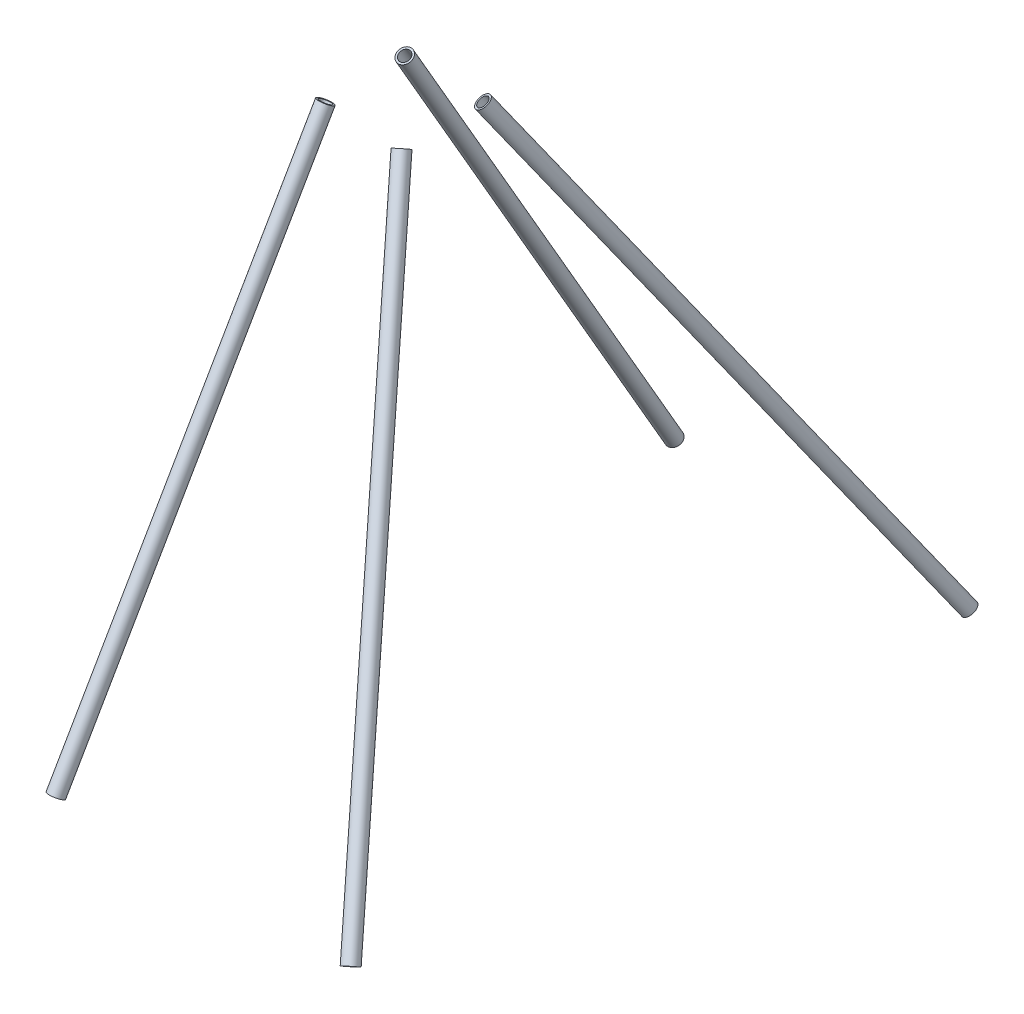
SolidWorks part; units mm, degrees
material "6061-T6 (SS)"
ref_plane "Front Plane" through (0, 0, 0) normal (0, 0, 1) x (1, 0, 0)
ref_plane "Top Plane" through (0, 0, 0) normal (0, 1, 0) x (1, 0, 0)
ref_plane "Right Plane" through (0, 0, 0) normal (1, 0, 0) x (0, 0, -1)
sketch "Sketch1" plane through (0, 0, 0) normal (1, 0, 0) x (0, 0, -1)
  line L0 (-31.75, 0) -> (31.75, 0) construction
  line L1 (31.75, 0) -> (266.7, -406.4)
  line L3 (-31.75, 0) -> (-266.7, -406.4)
  dimension "D1" = 406.4
  dimension "D2" = 533.4
  dimension "D3" = 63.5
ref_plane "Plane1" through (0, -406.4, 0) normal (0, 1, 0) x (1, 0, 0)
sketch "Sketch2" plane through (0, -406.4, 0) normal (0, 1, 0) x (1, 0, 0)
  line L0 (0, -266.7) -> (254, -266.7) construction
  line L2 (0, 266.7) -> (254, 266.7) construction
  dimension "D1" = 254
sketch "Sketch3" plane through (0, 0, 0) normal (0, 1, 0) x (1, 0, 0)
  line L1 (0, -31.75) -> (63.5, -31.75) construction
  line L2 (0, -31.75) -> (0, 31.75) construction
  line L3 (0, 31.75) -> (63.5, 31.75) construction
  line L4 (63.5, -31.75) -> (63.5, 31.75) construction
  dimension "D1" = 63.5
sketch3d "3DSketch1"
  line L0 (254, -406.4, 266.7) -> (63.5, 0, 31.75)
  line L1 (63.5, 0, -31.75) -> (254, -406.4, -266.7)
ref_plane "Plane2" through (0, -406.4, 266.7) normal (0, -0.8657, 0.5005) x (-1, 0, 0)
sketch "Sketch4" plane through (0, -406.4, 266.7) normal (0, -0.8657, 0.5005) x (-1, 0, 0)
  circle A0 centre (0, 0) radius 6.35
  circle A1 centre (0, 0) radius 4.699
  dimension "D1" = 12.7
  dimension "D2" = 9.398
extrude "Boss-Extrude1" add sketch "Sketch4" against normal blind 460.375 from offset 4.7625 contours A0 A1 offset against normal yes
ref_plane "Plane3" through (254, -406.4, 266.7) normal (-0.376, 0.8022, -0.4638) x (0.9266, 0.3255, -0.1882)
sketch "Sketch5" plane through (254, -406.4, 266.7) normal (-0.376, 0.8022, -0.4638) x (0.9266, 0.3255, -0.1882)
  circle A0 centre (0, 0) radius 6.35
  circle A1 centre (0, 0) radius 4.699
  dimension "D1" = 12.7
  dimension "D2" = 9.398
extrude "Boss-Extrude2" add sketch "Sketch5" along normal blind 495.3 from offset 4.7625 separate body
mirror "Mirror1" about plane through (0, 0, 0) normal (0, 0, 1) of bodies 101 102
